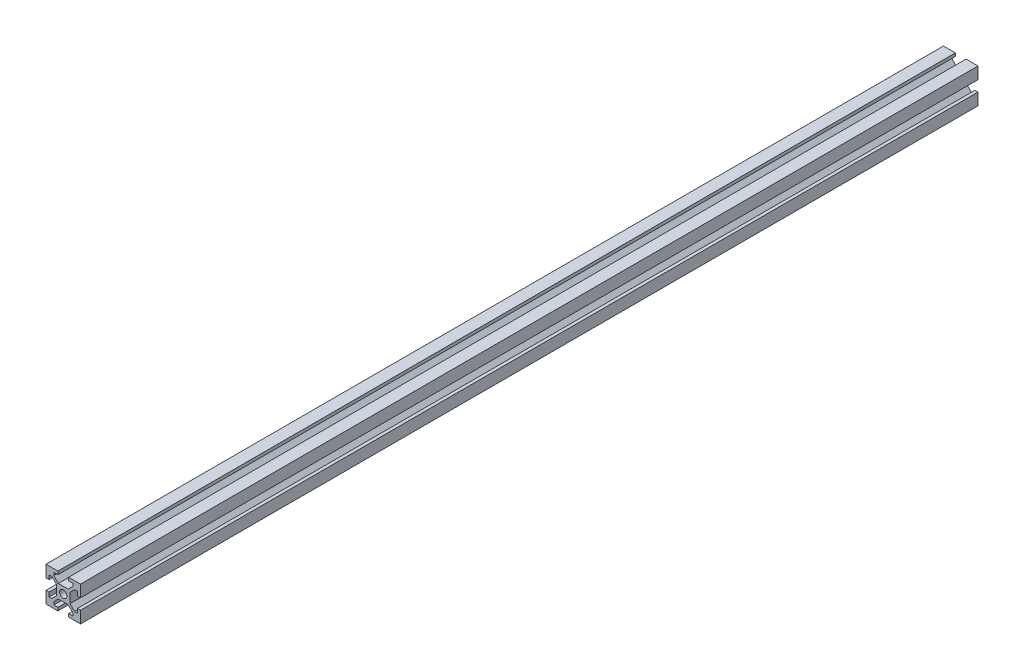
SolidWorks part; units mm, degrees
ref_plane "Front Plane" through (0, 0, 0) normal (0, 0, 1) x (1, 0, 0)
ref_plane "Top Plane" through (0, 0, 0) normal (0, 1, 0) x (1, 0, 0)
ref_plane "Right Plane" through (0, 0, 0) normal (1, 0, 0) x (0, 0, -1)
sketch "Sketch1" plane through (0, 0, 0) normal (0, 0, 1) x (1, 0, 0)
  line L0 (-3.1, 10) -> (-3.1, 8.2007)
  line L1 (-10, 10) -> (-3.1, 10)
  line L2 (-10, 10) -> (-10, 3.1)
  line L3 (-10, -10) -> (-3.1, -10)
  line L4 (10, 10) -> (10, 3.1)
  line L5 (-10, 10) -> (10, -10) construction
  line L6 (-10, -10) -> (10, 10) construction
  line L7 (-3.1, 8.2007) -> (-5.5, 8.2007)
  line L8 (-5.5, 8.2007) -> (-5.5, 6.5607)
  line L9 (-5.5, 6.5607) -> (-2.84, 3.9007)
  line L10 (-2.84, 3.9007) -> (2.84, 3.9007)
  line L11 (2.84, 3.9007) -> (5.5, 6.5607)
  line L12 (5.5, 6.5607) -> (5.5, 8.2007)
  line L13 (5.5, 8.2007) -> (3.1, 8.2007)
  line L14 (3.1, 8.2007) -> (3.1, 10)
  line L15 (-3.1, 8.2007) -> (3.1, 8.2007) construction
  line L16 (-5.5, 6.5607) -> (5.5, 6.5607) construction
  line L17 (3.1, 10) -> (10, 10)
  line L18 (8.2007, 3.1) -> (8.2007, 5.5)
  line L19 (8.2007, 5.5) -> (6.5607, 5.5)
  line L20 (6.5607, 5.5) -> (3.9007, 2.84)
  line L21 (3.9007, 2.84) -> (3.9007, -2.84)
  line L22 (3.9007, -2.84) -> (6.5607, -5.5)
  line L23 (6.5607, -5.5) -> (8.2007, -5.5)
  line L24 (8.2007, -5.5) -> (8.2007, -3.1)
  line L25 (8.2007, 3.1) -> (8.2007, -3.1) construction
  line L26 (6.5607, 5.5) -> (6.5607, -5.5) construction
  line L27 (10, 3.1) -> (8.2007, 3.1)
  line L28 (8.2007, -3.1) -> (10, -3.1)
  line L29 (3.1, -8.2007) -> (5.5, -8.2007)
  line L30 (5.5, -8.2007) -> (5.5, -6.5607)
  line L31 (5.5, -6.5607) -> (2.84, -3.9007)
  line L32 (2.84, -3.9007) -> (-2.84, -3.9007)
  line L33 (-2.84, -3.9007) -> (-5.5, -6.5607)
  line L34 (-5.5, -6.5607) -> (-5.5, -8.2007)
  line L35 (-5.5, -8.2007) -> (-3.1, -8.2007)
  line L36 (3.1, -8.2007) -> (-3.1, -8.2007) construction
  line L37 (5.5, -6.5607) -> (-5.5, -6.5607) construction
  line L38 (3.1, -10) -> (3.1, -8.2007)
  line L39 (-3.1, -8.2007) -> (-3.1, -10)
  line L40 (-8.2007, -3.1) -> (-8.2007, -5.5)
  line L41 (-8.2007, -5.5) -> (-6.5607, -5.5)
  line L42 (-6.5607, -5.5) -> (-3.9007, -2.84)
  line L43 (-3.9007, -2.84) -> (-3.9007, 2.84)
  line L44 (-3.9007, 2.84) -> (-6.5607, 5.5)
  line L45 (-6.5607, 5.5) -> (-8.2007, 5.5)
  line L46 (-8.2007, 5.5) -> (-8.2007, 3.1)
  line L47 (-8.2007, -3.1) -> (-8.2007, 3.1) construction
  line L48 (-6.5607, -5.5) -> (-6.5607, 5.5) construction
  line L49 (-10, -3.1) -> (-8.2007, -3.1)
  line L50 (-8.2007, 3.1) -> (-10, 3.1)
  line L51 (10, -3.1) -> (10, -10)
  line L52 (3.1, -10) -> (10, -10)
  line L53 (-10, -3.1) -> (-10, -10)
  point P0 (0, 0)
  point P8 (0, 8.2007)
  point P18 (0, 3.9007)
  dimension "D1" = 20
  dimension "D2" = 20
  dimension "D3" = 5.68
  dimension "D4" = 6.2
  dimension "D5" = 4.3
  dimension "D6" = 11
  dimension "D7" = 0.75
  dimension "D8" = 4
extrude "Boss-Extrude1" add sketch "Sketch1" along normal blind 520
sketch "Sketch2" plane through (0, 0, 520) normal (0, 0, 1) x (1, 0, 0)
  circle A0 centre (0, 0) radius 2.1
  dimension "D1" = 4.2
extrude "Cut-Extrude1" cut sketch "Sketch2" against normal through all
sketch "Sketch3" plane through (0, 3.9007, 0) normal (0, 1, 0) x (1, 0, 0)
  line L0 (0, 0) -> (0, -520) construction
  line L1 (2.84, -520) -> (-2.84, -520) construction
  circle A0 centre (0, -260) radius 2.1
  dimension "D1" = 4.2
extrude "Cut-Extrude2" cut sketch "Sketch3" against normal through all
